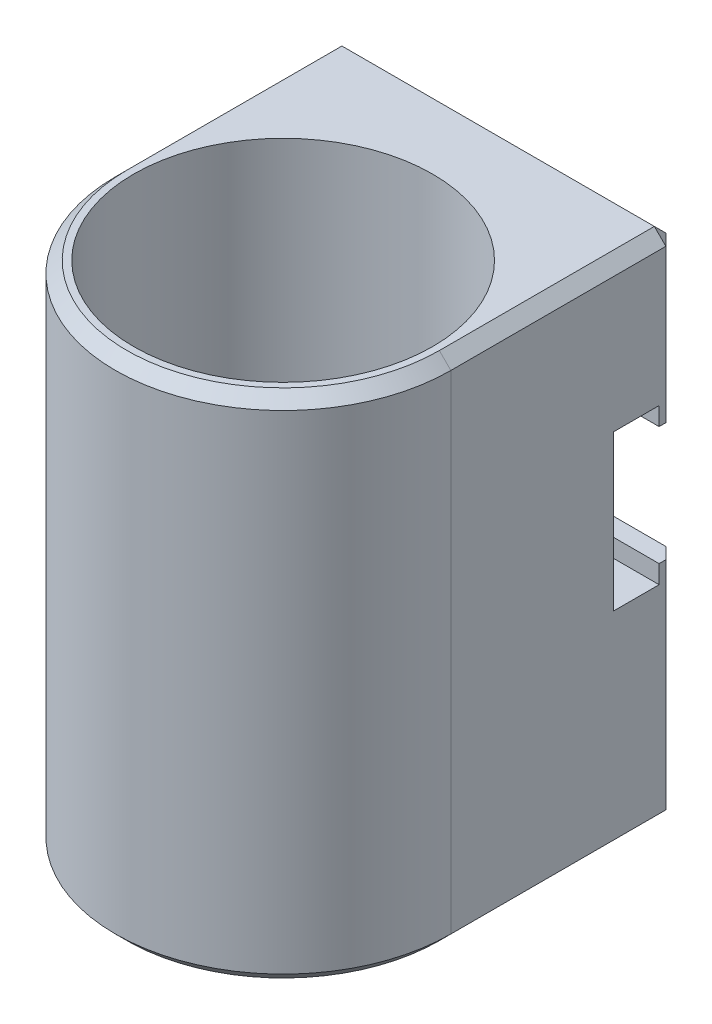
SolidWorks part; units mm, degrees
ref_plane "Front Plane" through (0, 0, 0) normal (0, 0, 1) x (1, 0, 0)
ref_plane "Top Plane" through (0, 0, 0) normal (0, 1, 0) x (1, 0, 0)
ref_plane "Right Plane" through (0, 0, 0) normal (1, 0, 0) x (0, 0, -1)
sketch "Sketch1" plane through (0, 0, 0) normal (0, 1, 0) x (1, 0, 0)
  line L0 (-14.5875, 0) -> (-14.5875, 19.7)
  line L1 (-14.5875, 19.7) -> (14.5875, 19.7)
  line L2 (14.5875, 19.7) -> (14.5875, 0)
  circle A0 centre (0, 0) radius 13
  circle A1 centre (0, 0) radius 14.5875 construction
  arc A2 (-14.5875, 0) -> (14.5875, 0) centre (0, 0) ccw
  dimension "D1" = 26
  dimension "D2" = 1.5875
  dimension "D3" = 19.7
extrude "Boss-Extrude1" add sketch "Sketch1" along normal blind 44.45
sketch "Sketch3" plane through (14.5875, 0, 0) normal (1, 0, 0) x (0, 0, -1)
  line L0 (19.7, 30.1625) -> (18.1125, 30.1625)
  line L1 (19.7, 44.45) -> (19.7, 0) construction
  line L2 (18.1125, 30.1625) -> (18.1125, 31.75)
  line L3 (18.1125, 31.75) -> (14.1438, 31.75)
  line L4 (14.1438, 31.75) -> (14.1438, 18.2563)
  line L5 (14.1438, 18.2563) -> (18.1125, 18.2563)
  line L6 (18.1125, 18.2563) -> (18.1125, 19.8438)
  line L7 (18.1125, 19.8438) -> (19.7, 19.8438)
  line L8 (19.7, 19.8438) -> (19.7, 30.1625)
  line L9 (0, 44.45) -> (19.7, 44.45) construction
  dimension "D1" = 1.5875
  dimension "D2" = 3.9688
  dimension "D3" = 13.4937
  dimension "D4" = 1.5875
  dimension "D5" = 12.7
extrude "Cut-Extrude1" cut sketch "Sketch3" against normal through all
chamfer "Chamfer1" distance 1 angle 45 12 edges at (-14.5875, 9.9219, -19.7) (14.5875, 9.9219, -19.7) (0, 0, -19.7) (-14.5875, 0, -9.85) (0, 0, 14.5875) (14.5875, 0, -9.85) (14.5875, 37.3062, -19.7) (-14.5875, 37.3062, -19.7) (0, 44.45, -19.7) (-14.5875, 44.45, -9.85) (14.5875, 44.45, -9.85) (0, 44.45, 14.5875)
